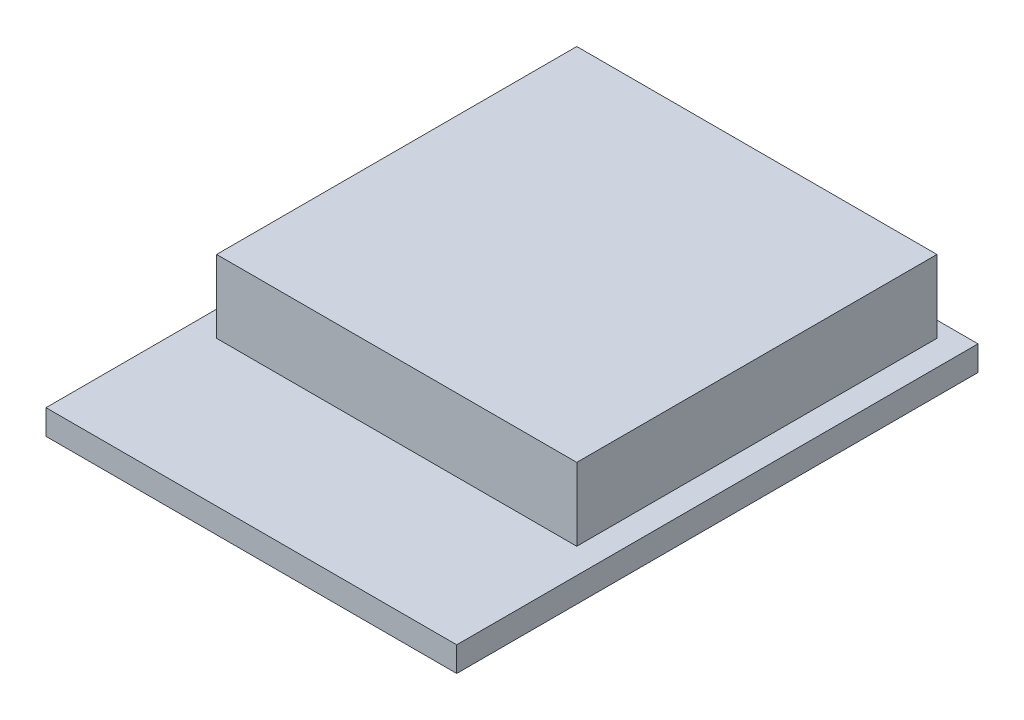
SolidWorks part; units mm, degrees
ref_plane "Front Plane" through (0, 0, 0) normal (0, 0, 1) x (1, 0, 0)
ref_plane "Top Plane" through (0, 0, 0) normal (0, 1, 0) x (1, 0, 0)
ref_plane "Right Plane" through (0, 0, 0) normal (1, 0, 0) x (0, 0, -1)
sketch "Sketch1" plane through (0, 0, 0) normal (0, 1, 0) x (1, 0, 0)
  line L1 (6.5, 8.25) -> (-6.5, 8.25)
  line L2 (6.5, 8.25) -> (6.5, -8.25)
  line L3 (6.5, -8.25) -> (-6.5, -8.25)
  line L4 (-6.5, 8.25) -> (-6.5, -8.25)
  line L5 (6.5, 8.25) -> (-6.5, -8.25) construction
  line L6 (6.5, -8.25) -> (-6.5, 8.25) construction
  point P0 (0, 0)
  dimension "D1" = 16.5
  dimension "D2" = 13
extrude "Boss-Extrude1" add sketch "Sketch1" along normal blind 0.7874
sketch "Sketch2" plane through (0, 0.7874, 0) normal (0, 1, 0) x (1, 0, 0)
  line L0 (6.5, 8.25) -> (-6.5, 8.25) construction
  line L1 (5.7, 7.75) -> (-5.7, 7.75)
  line L2 (5.7, 7.75) -> (5.7, -3.65)
  line L3 (5.7, -3.65) -> (-5.7, -3.65)
  line L4 (-5.7, 7.75) -> (-5.7, -3.65)
  line L5 (5.7, 7.75) -> (-5.7, -3.65) construction
  line L6 (5.7, -3.65) -> (-5.7, 7.75) construction
  line L7 (0, 0) -> (0, 2.05) construction
  point P0 (0, 0)
  dimension "D1" = 11.4
  dimension "D2" = 11.4
  dimension "D3" = 0.5
extrude "Boss-Extrude2" add sketch "Sketch2" along normal blind 2.3
